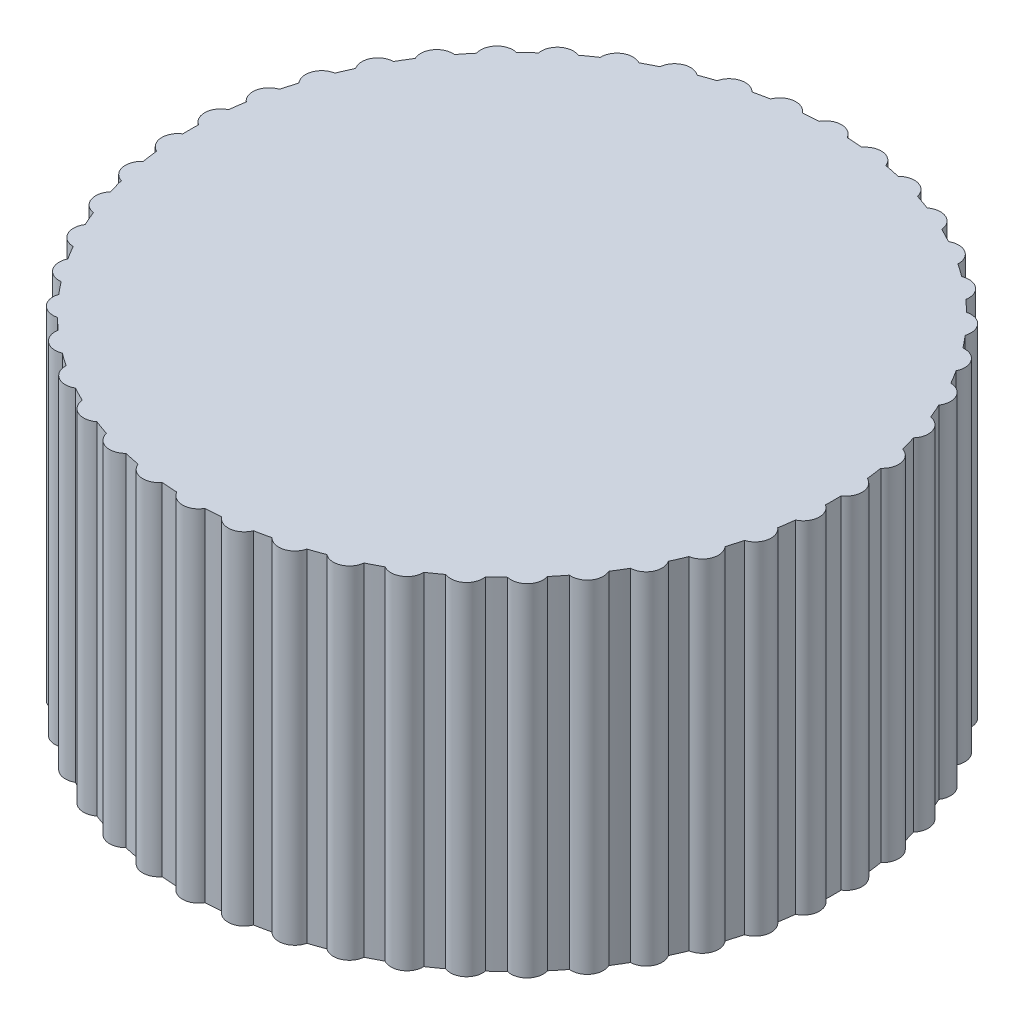
SolidWorks part; units mm, degrees
ref_plane "Front Plane" through (0, 0, 0) normal (0, 0, 1) x (1, 0, 0)
ref_plane "Top Plane" through (0, 0, 0) normal (0, 1, 0) x (1, 0, 0)
ref_plane "Right Plane" through (0, 0, 0) normal (1, 0, 0) x (0, 0, -1)
sketch "Sketch1" plane through (0, 0, 0) normal (0, 1, 0) x (1, 0, 0)
  line L1 (5.7735, 0) -> (2.8868, 5)
  line L2 (2.8868, 5) -> (-2.8868, 5)
  line L3 (-2.8868, 5) -> (-5.7735, 0)
  line L4 (-5.7735, 0) -> (-2.8868, -5)
  line L5 (-2.8868, -5) -> (2.8868, -5)
  line L6 (2.8868, -5) -> (5.7735, 0)
  circle A0 centre (0, 0) radius 8
  circle A1 centre (0, 0) radius 5 construction
extrude "Boss-Extrude1" add sketch "Sketch1" along normal blind 4
sketch "Sketch3" plane through (0, 4, 0) normal (0, 1, 0) x (1, 0, 0)
  circle A0 centre (0, 0) radius 8
extrude "Boss-Extrude3" add sketch "Sketch3" along normal blind 4.5
sketch "Sketch2" plane through (0, 8.5, 0) normal (0, 1, 0) x (1, 0, 0)
  line L0 (0, 8) -> (0, 7.8) construction
  circle A163 centre (0, 0) radius 8 construction
  circle A164 centre (0, 7.8) radius 0.4
  circle A165 centre (1.0621, 7.7274) radius 0.4
  circle A166 centre (2.1044, 7.5108) radius 0.4
  circle A167 centre (3.1075, 7.1542) radius 0.4
  circle A168 centre (4.0528, 6.6645) radius 0.4
  circle A169 centre (4.9225, 6.0505) radius 0.4
  circle A170 centre (5.7005, 5.3239) radius 0.4
  circle A171 centre (6.3724, 4.4981) radius 0.4
  circle A172 centre (6.9255, 3.5885) radius 0.4
  circle A173 centre (7.3496, 2.6121) radius 0.4
  circle A174 centre (7.6369, 1.587) radius 0.4
  circle A175 centre (7.7818, 0.5323) radius 0.4
  circle A176 centre (7.7818, -0.5323) radius 0.4
  circle A177 centre (7.6369, -1.587) radius 0.4
  circle A178 centre (7.3496, -2.6121) radius 0.4
  circle A179 centre (6.9255, -3.5885) radius 0.4
  circle A180 centre (6.3724, -4.4981) radius 0.4
  circle A181 centre (5.7005, -5.3239) radius 0.4
  circle A182 centre (4.9225, -6.0505) radius 0.4
  circle A183 centre (4.0528, -6.6645) radius 0.4
  circle A184 centre (3.1075, -7.1542) radius 0.4
  circle A185 centre (2.1044, -7.5108) radius 0.4
  circle A186 centre (1.0621, -7.7274) radius 0.4
  circle A187 centre (0, -7.8) radius 0.4
  circle A188 centre (-1.0621, -7.7274) radius 0.4
  circle A189 centre (-2.1044, -7.5108) radius 0.4
  circle A190 centre (-3.1075, -7.1542) radius 0.4
  circle A191 centre (-4.0528, -6.6645) radius 0.4
  circle A192 centre (-4.9225, -6.0505) radius 0.4
  circle A193 centre (-5.7005, -5.3239) radius 0.4
  circle A194 centre (-6.3724, -4.4981) radius 0.4
  circle A195 centre (-6.9255, -3.5885) radius 0.4
  circle A196 centre (-7.3496, -2.6121) radius 0.4
  circle A197 centre (-7.6369, -1.587) radius 0.4
  circle A198 centre (-7.7818, -0.5323) radius 0.4
  circle A199 centre (-7.7818, 0.5323) radius 0.4
  circle A200 centre (-7.6369, 1.587) radius 0.4
  circle A201 centre (-7.3496, 2.6121) radius 0.4
  circle A202 centre (-6.9255, 3.5885) radius 0.4
  circle A203 centre (-6.3724, 4.4981) radius 0.4
  circle A204 centre (-5.7005, 5.3239) radius 0.4
  circle A205 centre (-4.9225, 6.0505) radius 0.4
  circle A206 centre (-4.0528, 6.6645) radius 0.4
  circle A207 centre (-3.1075, 7.1542) radius 0.4
  circle A208 centre (-2.1044, 7.5108) radius 0.4
  circle A209 centre (-1.0621, 7.7274) radius 0.4
  point P100 (0, 0)
extrude "Boss-Extrude2" add sketch "Sketch2" against normal through all
